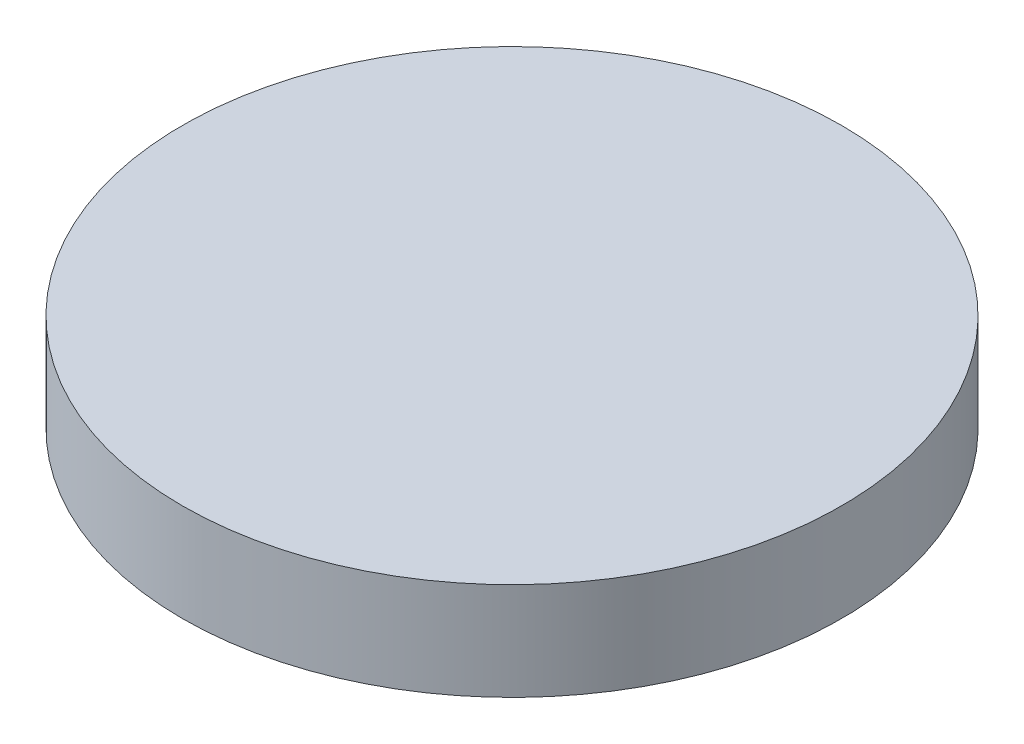
SolidWorks part; units mm, degrees
ref_plane "정면" through (0, 0, 0) normal (0, 0, 1) x (1, 0, 0)
ref_plane "윗면" through (0, 0, 0) normal (0, 1, 0) x (1, 0, 0)
ref_plane "우측면" through (0, 0, 0) normal (1, 0, 0) x (0, 0, -1)
sketch "스케치1" plane through (0, 0, 0) normal (0, 1, 0) x (1, 0, 0)
  circle A0 centre (0, 0) radius 13.5
  dimension "D1" = 27
extrude "보스-돌출1" add sketch "스케치1" along normal blind 4
